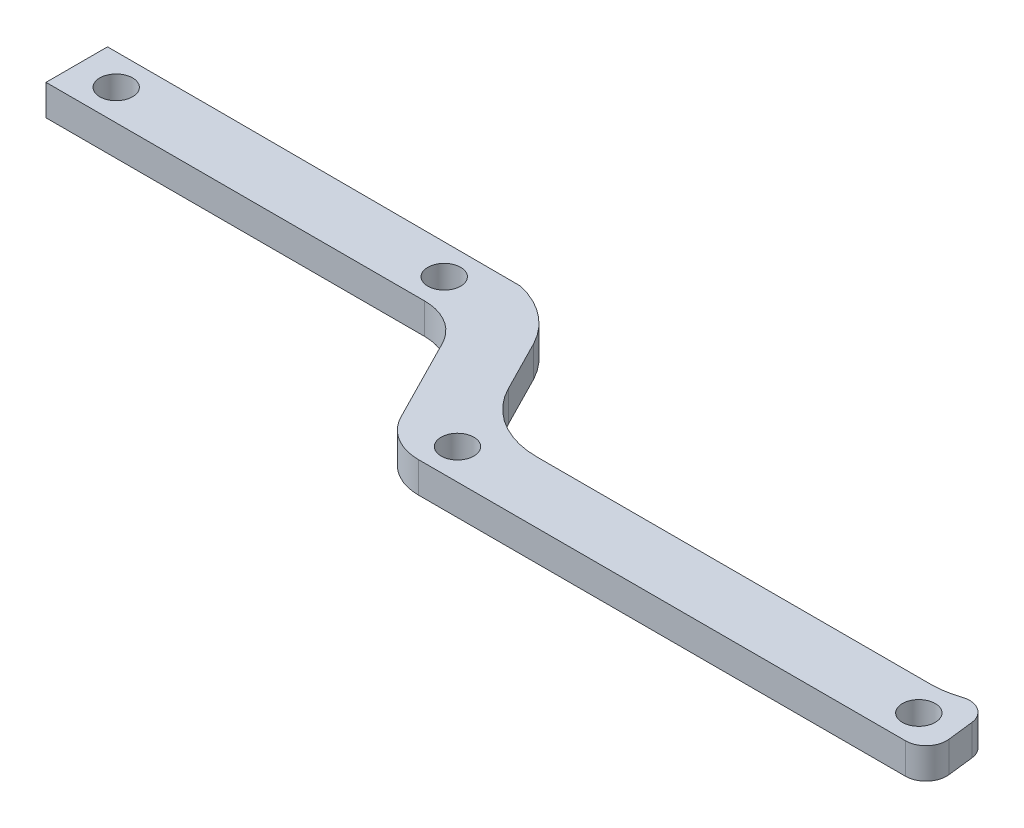
SolidWorks part; units mm, degrees
ref_plane "Спереди" through (0, 0, 0) normal (0, 0, 1) x (1, 0, 0)
ref_plane "Сверху" through (0, 0, 0) normal (0, 1, 0) x (1, 0, 0)
ref_plane "Справа" through (0, 0, 0) normal (1, 0, 0) x (0, 0, -1)
sketch "Эскиз1" plane through (0, 0, 0) normal (0, 1, 0) x (1, 0, 0)
  line L0 (0, 20) -> (0, -20) construction
  line L1 (16, 6.5) -> (40, 6.5)
  line L2 (-40, 14.5) -> (-16, 14.5)
  line L3 (-40, 14.5) -> (-40, 1.5)
  line L4 (-40, 1.5) -> (-16, 1.5)
  line L5 (-16, 14.5) -> (-16, 1.5)
  line L6 (-40, 14.5) -> (-16, 1.5) construction
  line L7 (-40, 1.5) -> (-16, 14.5) construction
  line L8 (-40, -1.5) -> (-16, -1.5)
  line L9 (-40, -1.5) -> (-40, -14.5)
  line L10 (-40, -14.5) -> (-16, -14.5)
  line L11 (-16, -1.5) -> (-16, -14.5)
  line L12 (-40, -1.5) -> (-16, -14.5) construction
  line L13 (-40, -14.5) -> (-16, -1.5) construction
  line L14 (-28, 8) -> (-28, -8) construction
  line L15 (0, 20) -> (-56.8521, 20) construction
  line L16 (0, 20) -> (59.9648, 20) construction
  line L17 (0, -20) -> (57.5525, -20) construction
  line L18 (0, -20) -> (-56.8521, -20) construction
  line L19 (16, 6.5) -> (16, -6.5)
  line L20 (16, -6.5) -> (40, -6.5)
  line L21 (40, 6.5) -> (40, -6.5)
  line L22 (16, 6.5) -> (40, -6.5) construction
  line L23 (16, -6.5) -> (40, 6.5) construction
  line L24 (28, 20) -> (28, -20) construction
  line L25 (-56.8521, 14) -> (93.1479, 14) construction
  line L26 (-56.8521, -16) -> (93.1479, -16) construction
  line L27 (-40, -37) -> (-56, -37) construction
  line L28 (-40, -37) -> (-24, -37) construction
  line L29 (-40, -14.5) -> (-40, -37) construction
  line L30 (-59.8465, -34) -> (-19.8465, -34) construction
  line L31 (-19.8465, -34) -> (-19.8465, -40) construction
  line L32 (-19.8465, -40) -> (-59.8465, -40) construction
  line L33 (-59.8465, -40) -> (-59.8465, -34) construction
  line L34 (-59.8465, -34) -> (-49.8878, 18)
  line L35 (36.6127, 18) -> (-49.8878, 18)
  line L36 (36.6127, 18) -> (75.1122, 5.9202)
  line L37 (-47.6771, -24.9007) -> (-49.0001, -34)
  line L38 (50, -16) -> (70, -16) construction
  line L39 (-59.8465, -34) -> (-59.8465, -40)
  line L40 (-59.8465, -40) -> (-19.8465, -40)
  line L41 (-19.8465, -40) -> (-14.2549, -50.9742)
  line L42 (-9.7998, -53.7042) -> (38.319, -53.7042)
  line L43 (75.1122, 5.9202) -> (75.1122, -16.0798)
  line L44 (50, 2) -> (50, -16) construction
  line L45 (-4.2859, -47.7018) -> (34.1658, -47.7018)
  line L46 (-49.0001, -34) -> (-22.2977, -34)
  line L47 (-13.9887, -38.2804) -> (-11.4139, -43.3337)
  line L48 (-41.7786, -20) -> (46.0945, -20)
  line L49 (40.7412, -44.2586) -> (51.0261, -29.4176)
  line L50 (-20.5914, -50.7042) -> (71.7063, -50.7042) construction
  line L51 (-20.5914, -53.7042) -> (73.7938, -53.7042) construction
  line L52 (0, -16) -> (0, -104.4432) construction
  line L53 (-47, 14) -> (-47, -16) construction
  line L54 (50, 2) -> (70, -16) construction
  line L55 (-44.6457, 8) -> (-11.6511, 8) construction
  line L56 (-47.6771, -8) -> (-3.6396, -8) construction
  line L57 (8, 0) -> (46.0945, 0) construction
  line L58 (50, 2) -> (70, 2) construction
  line L59 (75.1122, -16.0798) -> (41.2457, -52.4308)
  line L60 (-49.0001, -34) -> (-49.0001, -40) construction
  line L61 (-22.2977, -34) -> (-19.8465, -34)
  circle A0 centre (-8, 14) radius 1.6
  circle A1 centre (8, 14) radius 1.6
  circle A2 centre (-8, -16) radius 1.6
  circle A3 centre (8, -16) radius 1.6
  circle A4 centre (-47, 14) radius 1.6
  circle A5 centre (70, 2) radius 1.6
  circle A6 centre (50, 2) radius 1.6
  circle A7 centre (18, 14) radius 1.6
  circle A8 centre (-47, -16) radius 1.6
  circle A9 centre (-56, -37) radius 1.6
  circle A10 centre (-24, -37) radius 1.6
  circle A11 centre (50, -16) radius 1.6
  circle A12 centre (70, -16) radius 1.6
  arc A13 (-41.7786, -20) -> (-47.6771, -24.9007) centre (-41.7786, -26) ccw
  arc A14 (-19.8465, -34) -> (-13.9887, -38.2804) centre (-21.3286, -42.1767) cw
  arc A15 (-4.2859, -47.7018) -> (-11.4139, -43.3337) centre (-4.2859, -39.7018) cw
  arc A16 (40.7412, -44.2586) -> (34.1658, -47.7018) centre (34.1658, -39.7018) cw
  arc A17 (51.0261, -29.4176) -> (46.0945, -20) centre (46.0945, -26) ccw
  arc A18 (41.2457, -52.4308) -> (38.319, -53.7042) centre (38.319, -49.7042) cw
  arc A19 (-9.7998, -53.7042) -> (-14.2549, -50.9742) centre (-9.7998, -48.7042) cw
  circle A20 centre (-9, -50.7042) radius 1.6
  circle A21 centre (36, -50.7042) radius 1.6
  circle A22 centre (60, -7) radius 1.6
  circle A23 centre (-42, -8) radius 1
  circle A24 centre (-14, -8) radius 1
  circle A25 centre (-42, 8) radius 1
  circle A26 centre (-14, 8) radius 1
  circle A27 centre (14, 0) radius 1
  circle A28 centre (42, 0) radius 1
  point P2 (-28, 8)
  point P7 (0, 0)
  point P10 (28, 0)
  point P11 (-28, -8)
  point P35 (0, 14)
  point P41 (0, -16)
  point P77 (-46.7637, -20)
  point P86 (40.0593, -53.7042)
  point P92 (-49.0001, -34)
  dimension "D10" = 16
  dimension "D12" = 16
  dimension "D14" = 10
  dimension "D18" = 40
  dimension "D23" = 20
  dimension "D26" = 6
  dimension "D31" = 125
  dimension "D32" = 3
  dimension "D33" = 45
  dimension "D36" = 28
  dimension "D21" = 4
  dimension "D1" = 13
  dimension "D2" = 24
  dimension "D3" = 28
  dimension "D4" = 28
  dimension "D5" = 20
  dimension "D6" = 12
  dimension "D7" = 3
  dimension "D8" = 6
  dimension "D9" = 4
  dimension "D11" = 8
  dimension "D13" = 8
  dimension "D15" = 20
  dimension "D16" = 50
  dimension "D17" = 32
  dimension "D19" = 6
  dimension "D20" = 3
  dimension "D22" = 6.0024
  dimension "D24" = 12
  dimension "D25" = 36
  dimension "D27" = 6
  dimension "D29" = 14
  dimension "D30" = 22
  dimension "D34" = 40
  dimension "D35" = 47
  dimension "D37" = 28
  dimension "D38" = 28
  dimension "D39" = 14
  dimension "D40" = 14
  dimension "D41" = 14
  dimension "D42" = 18
  dimension "D43" = 2
extrude "Бобышка-Вытянуть1" add sketch "Эскиз1" along normal blind 3
sketch "Эскиз2" plane through (0, 0, 0) normal (0, 1, 0) x (1, 0, 0)
  line L0 (46.1017, 15.0227) -> (46.0945, -20)
  line L2 (75.1122, 5.9202) -> (36.6127, 18) construction
  line L4 (46.0945, -20) -> (71.46, -20)
  line L10 (0, 18) -> (0, -19.9611) construction
  line L11 (12, 8) -> (-12, 8)
  line L12 (12, 8) -> (12, 18)
  line L13 (12, 18) -> (-12, 18)
  line L14 (-12, 8) -> (-12, 18)
  line L15 (12, 8) -> (-12, 18) construction
  line L16 (12, 18) -> (-12, 8) construction
  line L17 (12, -19.9611) -> (-12, -19.9611)
  line L18 (12, -19.9611) -> (12, -9.9611)
  line L19 (12, -9.9611) -> (-12, -9.9611)
  line L20 (-12, -19.9611) -> (-12, -9.9611)
  line L21 (12, -19.9611) -> (-12, -9.9611) construction
  line L22 (12, -9.9611) -> (-12, -19.9611) construction
  line L24 (75.1122, -16.0798) -> (75.1122, 5.9202)
  line L25 (41.2457, -52.4308) -> (75.1122, -16.0798) construction
  line L26 (71.46, -20) -> (75.1122, -16.0798)
  line L27 (46.1017, 15.0227) -> (75.1122, 5.9202)
  line L28 (36.6127, 18) -> (-49.8878, 18) construction
  circle A0 centre (50, 2) radius 1.6
  circle A1 centre (70, 2) radius 1.6
  circle A2 centre (70, -16) radius 1.6
  circle A3 centre (50, -16) radius 1.6
  circle A4 centre (-8, 14) radius 1.6
  circle A5 centre (8, 14) radius 1.6
  circle A6 centre (-8, -16) radius 1.6
  circle A7 centre (8, -16) radius 1.6
  circle A12 centre (60, -7) radius 1.6
  point P26 (0, 13)
  point P35 (0, -14.9611)
  point P65 (0, 18)
  dimension "D2" = 24
extrude "Бобышка-Вытянуть2" add sketch "Эскиз2" against normal blind 9
sketch "Эскиз3" plane through (75.1122, 0, 0) normal (1, 0, 0) x (0, 0, -1)
  line L0 (-16.0798, -9) -> (5.9202, -9) construction
  line L1 (-13.3846, -15) -> (-1.3846, -15) construction
  line L2 (-13.3846, -15) -> (-13.3846, -3) construction
  line L3 (-13.3846, -3) -> (-1.3846, -3) construction
  line L4 (-1.3846, -15) -> (-1.3846, -3) construction
  line L6 (-13.3846, -3) -> (-1.3846, -15) construction
  line L8 (-1.3846, -3) -> (-13.3846, -15) construction
  line L9 (-18.1996, 12.1365) -> (3.7449, 12.1365) construction
  circle A0 centre (-7.3846, -9) radius 6
  point P8 (-7.3846, -9)
  dimension "D1" = 12
extrude "Вырез-Вытянуть1" cut sketch "Эскиз3" against normal blind 20
sketch "Эскиз4" plane through (0, 0, -18) normal (0, 0, -1) x (-1, 0, 0)
  line L1 (-12, -9) -> (12, -9) construction
  circle A0 centre (0, -9) radius 4
extrude "Вырез-Вытянуть2" cut sketch "Эскиз4" against normal through all
sketch "Эскиз6" plane through (0, 0, -18) normal (0, 0, -1) x (-1, 0, 0)
  circle A0 centre (0, -9) radius 5.6
extrude "Вырез-Вытянуть3" cut sketch "Эскиз6" against normal blind 5
sketch "Эскиз7" plane through (0, 0, 19.9611) normal (0, 0, 1) x (1, 0, 0)
  circle A0 centre (0, -9) radius 5.6
extrude "Вырез-Вытянуть4" cut sketch "Эскиз7" against normal blind 6
fillet "Скругление5" radius 5 1 edges at (-49.8878, 1.5, -18)
fillet "Скругление6" radius 5 1 edges at (-19.8465, 1.5, 40)
sketch "Sketch1" plane through (0, 3, 0) normal (0, 1, 0) x (1, 0, 0)
  line L0 (-59.8465, -34) -> (-49.0001, -34)
  line L1 (-49.0001, -34) -> (58.179, -34.2553) construction
  line L2 (41.2457, -52.4308) -> (75.1122, -16.0798) construction
  line L3 (39.9148, -53.3721) -> (39.0527, -46.0357)
  line L4 (39.0527, -46.0357) -> (39.0527, -34.2098)
  line L5 (-49.0001, -34) -> (39.0527, -34.2098)
  arc A0 (38.319, -53.7042) -> (41.2457, -52.4308) centre (38.319, -49.7042) ccw construction
  arc A1 (34.1658, -47.7018) -> (40.7412, -44.2586) centre (34.1658, -39.7018) ccw construction
  arc A2 (-59.8465, -34) -> (39.9148, -53.3721) centre (7.555, 46.5416) cw
extrude "Cut-Extrude1" cut sketch "Sketch1" against normal through all
fillet "Fillet1" radius 2 2 edges at (39.9148, 1.5, 53.3721) (39.0527, 1.5, 46.0357)
